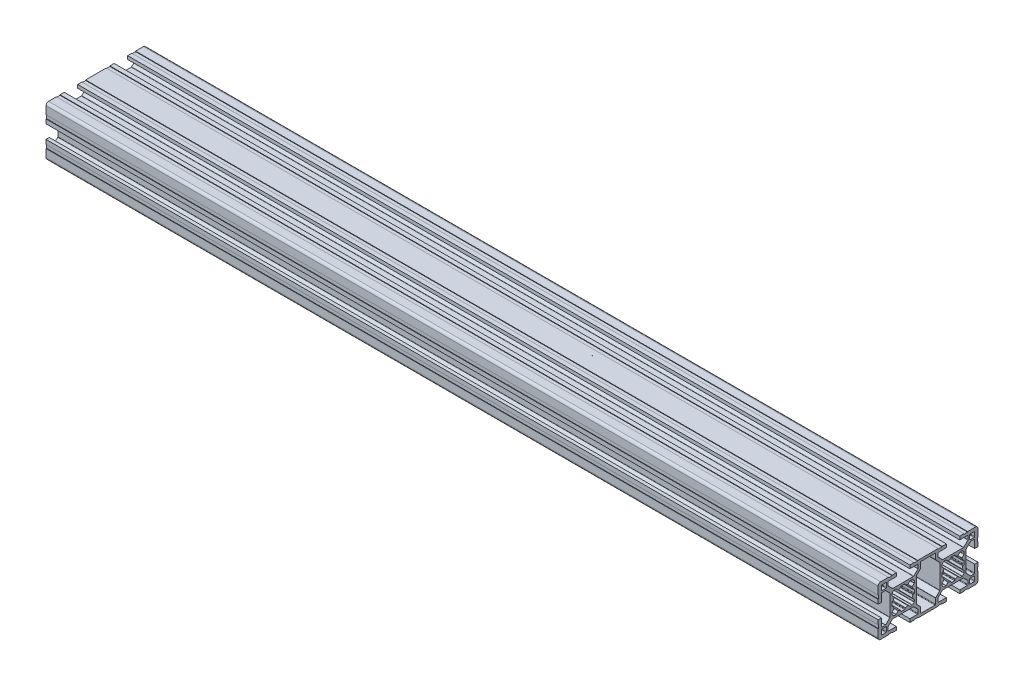
SolidWorks part; units mm, degrees
material "6063-T5 (Padrão)"
ref_plane "Plano frontal" through (0, 0, 0) normal (0, 0, 1) x (1, 0, 0)
ref_plane "Plano superior" through (0, 0, 0) normal (0, 1, 0) x (1, 0, 0)
ref_plane "Plano direito" through (0, 0, 0) normal (1, 0, 0) x (0, 0, -1)
sketch "Esboço1" plane through (0, 0, 0) normal (0, 0, 1) x (1, 0, 0)
  line L0 (-250, 0) -> (250, 0)
  point P4 (0, 0)
  dimension "D1" = 500
other "Retangular PF30-02 - PERFIL 3060 BÁSICO(1)"
ref_plane "Plano1" through (-250, 0, 0) normal (1, 0, 0) x (0, 1, 0)
sketch "Sketch11" plane through (-250, 0, 0) normal (1, 0, 0) x (0, 1, 0)
  line L0 (-9.8464, -4.5906) -> (-7.4222, -7.0149)
  line L1 (-7.21, -7.1028) -> (7.21, -7.1028)
  line L2 (7.4222, -7.0149) -> (9.8464, -4.5906)
  line L3 (10.0586, -4.5028) -> (13.2, -4.5028)
  line L4 (13.5, -4.2028) -> (13.5, 4.1972)
  line L5 (13.2, 4.4972) -> (10.0586, 4.4972)
  line L6 (9.8464, 4.5851) -> (7.4222, 7.0094)
  line L7 (7.21, 7.0972) -> (-7.21, 7.0972)
  line L8 (-7.4222, 7.0094) -> (-9.8464, 4.5851)
  line L9 (-10.0586, 4.4972) -> (-13.2, 4.4972)
  line L10 (-13.5, 4.1972) -> (-13.5, -4.2028)
  line L11 (-13.2, -4.5028) -> (-10.0586, -4.5028)
  line L12 (-6.7, 15.9528) -> (-6.7, 14.0528)
  line L13 (-6.1579, 16.2528) -> (-6.4, 16.2528)
  line L14 (-6.6121, 19.14) -> (-5.4871, 18.015)
  line L15 (-6.7, 20.4423) -> (-6.7, 19.3522)
  line L16 (-6.1319, 21.1347) -> (-6.6121, 20.6545)
  line L17 (-10.4678, 23.9149) -> (-7.9879, 21.435)
  line L18 (-12.7, 24.0028) -> (-10.6799, 24.0028)
  line L19 (-13, 19.0528) -> (-13, 23.7028)
  line L20 (-13, 19.0528) -> (-15, 19.0528)
  line L21 (6.7, 15.9528) -> (6.7, 14.0528)
  line L22 (7.9, 21.2229) -> (7.9, 8.7827)
  line L23 (15, 21.6028) -> (15, 19.0528)
  line L24 (-5.4396, 21.7028) -> (-4.3494, 21.7028)
  line L25 (-13, 25.3028) -> (-13, 27.7028)
  line L26 (-4.05, 28.0028) -> (-8.7, 28.0028)
  line L27 (-12.7, 28.0028) -> (-10.3, 28.0028)
  line L28 (-9, 27.7028) -> (-9, 25.6827)
  line L29 (-10, 27.7028) -> (-10, 25.3028)
  line L30 (-8.9121, 25.4705) -> (-6.4322, 22.9906)
  line L31 (15, 23.8028) -> (14.7, 23.8028)
  line L32 (14.7, 23.8028) -> (14.7, 21.6028)
  line L33 (15, 28.5028) -> (15, 23.8028)
  line L34 (8.8, 30.0028) -> (13.5, 30.0028)
  line L35 (8.8, 29.7028) -> (6.6, 29.7028)
  line L36 (4.05, 30.0028) -> (6.6, 30.0028)
  line L37 (4.05, 28.0028) -> (4.05, 30.0028)
  line L38 (10.3, 25.0028) -> (12.7, 25.0028)
  line L39 (15, 21.6028) -> (14.7, 21.6028)
  line L40 (6.6, 30.0028) -> (6.6, 29.7028)
  line L41 (-6.1319, 21.1347) -> (-5.6517, 21.6149)
  line L42 (-4.1373, 21.6149) -> (-3.0123, 20.4899)
  line L43 (-1.25, 21.1607) -> (-1.25, 21.4028)
  line L44 (8.8, 30.0028) -> (8.8, 29.7028)
  line L45 (1.25, 21.1607) -> (1.25, 21.4028)
  line L46 (4.1373, 21.6149) -> (3.0123, 20.4899)
  line L47 (6.1319, 21.1347) -> (5.6517, 21.6149)
  line L48 (8.9121, 25.4705) -> (6.4322, 22.9906)
  line L49 (10, 27.7028) -> (10, 25.3028)
  line L50 (9, 27.7028) -> (9, 25.6827)
  line L51 (12.7, 28.0028) -> (10.3, 28.0028)
  line L52 (4.05, 28.0028) -> (8.7, 28.0028)
  line L53 (13, 25.3028) -> (13, 27.7028)
  line L54 (5.4396, 21.7028) -> (4.3494, 21.7028)
  line L55 (13, 19.0528) -> (15, 19.0528)
  line L56 (13, 19.0528) -> (13, 23.7028)
  line L57 (12.7, 24.0028) -> (10.6799, 24.0028)
  line L58 (10.4678, 23.9149) -> (7.9879, 21.435)
  line L59 (6.1319, 21.1347) -> (6.6121, 20.6545)
  line L60 (6.7, 20.4423) -> (6.7, 19.3522)
  line L61 (6.6121, 19.14) -> (5.4871, 18.015)
  line L62 (6.1579, 16.2528) -> (6.4, 16.2528)
  line L63 (-7.9, 8.7827) -> (-7.9, 21.2229)
  line L64 (-0.95, 8.3028) -> (0.95, 8.3028)
  line L65 (-15, 8.4028) -> (-15, 10.9528)
  line L66 (-15, 6.2028) -> (-14.7, 6.2028)
  line L67 (-14.7, 6.2028) -> (-14.7, 8.4028)
  line L68 (-15, -14.9972) -> (15, -14.9972) construction
  line L69 (-6.1579, -13.7472) -> (-6.4, -13.7472)
  line L70 (-6.6121, -10.86) -> (-5.4871, -11.985)
  line L71 (-6.7, -9.5577) -> (-6.7, -10.6478)
  line L72 (-15, 8.4028) -> (-14.7, 8.4028)
  line L73 (-0.95, -21.6972) -> (0.95, -21.6972)
  line L74 (-6.1319, -8.8653) -> (-6.6121, -9.3455)
  line L75 (6.1579, 13.7528) -> (6.4, 13.7528)
  line L76 (6.6121, 10.8655) -> (5.4871, 11.9905)
  line L77 (6.7, 9.5632) -> (6.7, 10.6534)
  line L78 (6.1319, 8.8709) -> (6.6121, 9.3511)
  line L79 (10.4678, 6.0906) -> (7.9879, 8.5705)
  line L80 (12.7, 6.0028) -> (10.6799, 6.0028)
  line L81 (13, 10.9528) -> (13, 6.3028)
  line L82 (13, 10.9528) -> (15, 10.9528)
  line L83 (5.4396, 8.3028) -> (4.3494, 8.3028)
  line L84 (-10.4678, -6.0851) -> (-7.9879, -8.565)
  line L85 (-8.8, 30.0028) -> (-8.8, 29.7028)
  line L86 (-12.7, -5.9972) -> (-10.6799, -5.9972)
  line L87 (-13, -10.9472) -> (-13, -6.2972)
  line L88 (-13, -10.9472) -> (-15, -10.9472)
  line L89 (15, -8.3972) -> (15, -10.9472)
  line L90 (-5.4396, -8.2972) -> (-4.3494, -8.2972)
  line L91 (6.1319, 8.8709) -> (5.6517, 8.3906)
  line L92 (4.1373, 8.3906) -> (3.0123, 9.5156)
  line L93 (1.25, 8.8448) -> (1.25, 8.6028)
  line L94 (-15, -21.5972) -> (-15, -19.0472)
  line L95 (-6.6, 30.0028) -> (-6.6, 29.7028)
  line L96 (-1.25, 8.8448) -> (-1.25, 8.6028)
  line L97 (-4.1373, 8.3906) -> (-3.0123, 9.5156)
  line L98 (-6.1319, 8.8709) -> (-5.6517, 8.3906)
  line L99 (-15, -23.7972) -> (-14.7, -23.7972)
  line L100 (15, 8.4028) -> (14.7, 8.4028)
  line L101 (-14.7, -23.7972) -> (-14.7, -21.5972)
  line L102 (-15, -28.4972) -> (-15, -23.7972)
  line L103 (-8.8, -29.9972) -> (-13.5, -29.9972)
  line L104 (-8.8, -29.6972) -> (-6.6, -29.6972)
  line L105 (-4.05, -29.9972) -> (-6.6, -29.9972)
  line L106 (14.7, 6.2028) -> (14.7, 8.4028)
  line L107 (15, 6.2028) -> (14.7, 6.2028)
  line L108 (-4.05, -27.9972) -> (-4.05, -29.9972)
  line L109 (-10.3, -24.9972) -> (-12.7, -24.9972)
  line L110 (-6.2201, -22.8972) -> (6.2201, -22.8972)
  line L111 (-15, -21.5972) -> (-14.7, -21.5972)
  line L112 (15, -6.1972) -> (14.7, -6.1972)
  line L113 (-15, 21.6028) -> (-14.7, 21.6028)
  line L114 (-6.2201, 22.9028) -> (6.2201, 22.9028)
  line L115 (-10.3, 25.0028) -> (-12.7, 25.0028)
  line L116 (-4.05, 28.0028) -> (-4.05, 30.0028)
  line L117 (-4.05, 30.0028) -> (-6.6, 30.0028)
  line L118 (-8.8, 29.7028) -> (-6.6, 29.7028)
  line L119 (0, 29.9972) -> (0, -29.9972) construction
  line L120 (-15, 15.0028) -> (15, 15.0028) construction
  line L121 (-8.8, 30.0028) -> (-13.5, 30.0028)
  line L122 (-15, 28.5028) -> (-15, 23.8028)
  line L123 (-14.7, 23.8028) -> (-14.7, 21.6028)
  line L124 (-15, 23.8028) -> (-14.7, 23.8028)
  line L125 (-15, 21.6028) -> (-15, 19.0528)
  line L126 (14.7, -6.1972) -> (14.7, -8.3972)
  line L127 (-5.4396, 8.3028) -> (-4.3494, 8.3028)
  line L128 (15, 8.4028) -> (15, 10.9528)
  line L129 (15, 6.2028) -> (15, -6.1972)
  line L130 (-13, 10.9528) -> (-15, 10.9528)
  line L131 (-13, 10.9528) -> (-13, 6.3028)
  line L132 (-12.7, 6.0028) -> (-10.6799, 6.0028)
  line L133 (-10.4678, 6.0906) -> (-7.9879, 8.5705)
  line L134 (-6.1319, 8.8709) -> (-6.6121, 9.3511)
  line L135 (-0.95, 21.7028) -> (0.95, 21.7028)
  line L136 (-6.7, 9.5632) -> (-6.7, 10.6534)
  line L137 (-6.6121, 10.8655) -> (-5.4871, 11.9905)
  line L138 (-6.1579, 13.7528) -> (-6.4, 13.7528)
  line L139 (15, 0.0028) -> (-15, 0.0028) construction
  line L140 (15, -8.3972) -> (14.7, -8.3972)
  line L141 (-6.1319, -8.8653) -> (-5.6517, -8.3851)
  line L142 (-4.1373, -8.3851) -> (-3.0123, -9.5101)
  line L143 (-1.25, -8.8393) -> (-1.25, -8.5972)
  line L144 (-6.6, -29.9972) -> (-6.6, -29.6972)
  line L145 (1.25, -8.8393) -> (1.25, -8.5972)
  line L146 (4.1373, -8.3851) -> (3.0123, -9.5101)
  line L147 (6.1319, -8.8653) -> (5.6517, -8.3851)
  line L148 (-8.8, -29.9972) -> (-8.8, -29.6972)
  line L149 (5.4396, -8.2972) -> (4.3494, -8.2972)
  line L150 (13, -10.9472) -> (15, -10.9472)
  line L151 (13, -10.9472) -> (13, -6.2972)
  line L152 (12.7, -5.9972) -> (10.6799, -5.9972)
  line L153 (10.4678, -6.0851) -> (7.9879, -8.565)
  line L154 (6.1319, -8.8653) -> (6.6121, -9.3455)
  line L155 (6.7, -9.5577) -> (6.7, -10.6478)
  line L156 (6.6121, -10.86) -> (5.4871, -11.985)
  line L157 (6.1579, -13.7472) -> (6.4, -13.7472)
  line L158 (-15, -8.3972) -> (-14.7, -8.3972)
  line L159 (-15, 6.2028) -> (-15, -6.1972)
  line L160 (-14.7, -6.1972) -> (-14.7, -8.3972)
  line L161 (-15, -6.1972) -> (-14.7, -6.1972)
  line L162 (-15, -8.3972) -> (-15, -10.9472)
  line L163 (-0.95, -8.2972) -> (0.95, -8.2972)
  line L164 (-7.9, -8.7771) -> (-7.9, -21.2173)
  line L165 (6.1579, -16.2472) -> (6.4, -16.2472)
  line L166 (6.6121, -19.1345) -> (5.4871, -18.0095)
  line L167 (6.7, -20.4368) -> (6.7, -19.3466)
  line L168 (6.1319, -21.1291) -> (6.6121, -20.6489)
  line L169 (10.4678, -23.9094) -> (7.9879, -21.4295)
  line L170 (12.7, -23.9972) -> (10.6799, -23.9972)
  line L171 (13, -19.0472) -> (13, -23.6972)
  line L172 (13, -19.0472) -> (15, -19.0472)
  line L173 (5.4396, -21.6972) -> (4.3494, -21.6972)
  line L174 (13, -25.2972) -> (13, -27.6972)
  line L175 (4.05, -27.9972) -> (8.7, -27.9972)
  line L176 (12.7, -27.9972) -> (10.3, -27.9972)
  line L177 (9, -27.6972) -> (9, -25.6771)
  line L178 (10, -27.6972) -> (10, -25.2972)
  line L179 (8.9121, -25.465) -> (6.4322, -22.9851)
  line L180 (6.1319, -21.1291) -> (5.6517, -21.6093)
  line L181 (4.1373, -21.6093) -> (3.0123, -20.4844)
  line L182 (1.25, -21.1551) -> (1.25, -21.3972)
  line L183 (8.8, -29.9972) -> (8.8, -29.6972)
  line L184 (-1.25, -21.1551) -> (-1.25, -21.3972)
  line L185 (-4.1373, -21.6093) -> (-3.0123, -20.4844)
  line L186 (-6.1319, -21.1291) -> (-5.6517, -21.6093)
  line L187 (6.6, -29.9972) -> (6.6, -29.6972)
  line L188 (15, -21.5972) -> (14.7, -21.5972)
  line L189 (10.3, -24.9972) -> (12.7, -24.9972)
  line L190 (4.05, -27.9972) -> (4.05, -29.9972)
  line L191 (4.05, -29.9972) -> (6.6, -29.9972)
  line L192 (8.8, -29.6972) -> (6.6, -29.6972)
  line L193 (8.8, -29.9972) -> (13.5, -29.9972)
  line L194 (15, -28.4972) -> (15, -23.7972)
  line L195 (14.7, -23.7972) -> (14.7, -21.5972)
  line L196 (15, -23.7972) -> (14.7, -23.7972)
  line L197 (-8.9121, -25.465) -> (-6.4322, -22.9851)
  line L198 (-10, -27.6972) -> (-10, -25.2972)
  line L199 (-9, -27.6972) -> (-9, -25.6771)
  line L200 (-12.7, -27.9972) -> (-10.3, -27.9972)
  line L201 (-4.05, -27.9972) -> (-8.7, -27.9972)
  line L202 (-13, -25.2972) -> (-13, -27.6972)
  line L203 (-5.4396, -21.6972) -> (-4.3494, -21.6972)
  line L204 (15, -21.5972) -> (15, -19.0472)
  line L205 (7.9, -21.2173) -> (7.9, -8.7771)
  line L206 (6.7, -15.9472) -> (6.7, -14.0472)
  line L207 (-13, -19.0472) -> (-15, -19.0472)
  line L208 (-13, -19.0472) -> (-13, -23.6972)
  line L209 (-12.7, -23.9972) -> (-10.6799, -23.9972)
  line L210 (-10.4678, -23.9094) -> (-7.9879, -21.4295)
  line L211 (-6.1319, -21.1291) -> (-6.6121, -20.6489)
  line L212 (-6.7, -20.4368) -> (-6.7, -19.3466)
  line L213 (-6.6121, -19.1345) -> (-5.4871, -18.0095)
  line L214 (-6.1579, -16.2472) -> (-6.4, -16.2472)
  line L215 (-6.7, -15.9472) -> (-6.7, -14.0472)
  arc A0 (-9.8464, -4.5906) -> (-10.0586, -4.5028) centre (-10.0586, -4.8028) ccw
  arc A1 (-7.4222, -7.0149) -> (-7.21, -7.1028) centre (-7.21, -6.8028) ccw
  arc A2 (7.21, -7.1028) -> (7.4222, -7.0149) centre (7.21, -6.8028) ccw
  arc A3 (10.0586, -4.5028) -> (9.8464, -4.5906) centre (10.0586, -4.8028) ccw
  arc A4 (13.2, -4.5028) -> (13.5, -4.2028) centre (13.2, -4.2028) ccw
  arc A5 (13.5, 4.1972) -> (13.2, 4.4972) centre (13.2, 4.1972) ccw
  arc A6 (9.8464, 4.5851) -> (10.0586, 4.4972) centre (10.0586, 4.7972) ccw
  arc A7 (7.4222, 7.0094) -> (7.21, 7.0972) centre (7.21, 6.7972) ccw
  arc A8 (-7.21, 7.0972) -> (-7.4222, 7.0094) centre (-7.21, 6.7972) ccw
  arc A9 (-10.0586, 4.4972) -> (-9.8464, 4.5851) centre (-10.0586, 4.7972) ccw
  arc A10 (-13.2, 4.4972) -> (-13.5, 4.1972) centre (-13.2, 4.1972) ccw
  arc A11 (-13.5, -4.2028) -> (-13.2, -4.5028) centre (-13.2, -4.2028) ccw
  arc A12 (-6.4, 16.2528) -> (-6.7, 15.9528) centre (-6.4, 15.9528) ccw
  arc A13 (-5.867, 16.4795) -> (-6.1579, 16.2528) centre (-6.1579, 16.5528) cw
  arc A14 (-5.867, 16.4795) -> (-5.43, 17.6706) centre (0, 15.0028) cw
  arc A15 (-5.4871, 18.015) -> (-5.43, 17.6706) centre (-5.6993, 17.8029) cw
  arc A16 (-6.6121, 19.14) -> (-6.7, 19.3522) centre (-6.4, 19.3522) cw
  arc A17 (-6.6121, 20.6545) -> (-6.7, 20.4423) centre (-6.4, 20.4423) ccw
  arc A18 (-7.9879, 21.435) -> (-7.9, 21.2229) centre (-8.2, 21.2229) cw
  arc A19 (-10.6799, 24.0028) -> (-10.4678, 23.9149) centre (-10.6799, 23.7028) cw
  arc A20 (-13, 23.7028) -> (-12.7, 24.0028) centre (-12.7, 23.7028) cw
  arc A21 (13.5, 30.0028) -> (15, 28.5028) centre (13.5, 28.5028) cw
  arc A22 (1.25, 21.4028) -> (0.95, 21.7028) centre (0.95, 21.4028) ccw
  arc A23 (4.1373, 21.6149) -> (4.3494, 21.7028) centre (4.3494, 21.4028) cw
  arc A24 (1.4768, 20.8698) -> (1.25, 21.1607) centre (1.55, 21.1607) cw
  arc A25 (1.4768, 20.8698) -> (2.6678, 20.4328) centre (0, 15.0028) cw
  arc A26 (-10.3, 25.0028) -> (-10, 25.3028) centre (-10.3, 25.3028) ccw
  arc A27 (-6.4322, 22.9906) -> (-6.2201, 22.9028) centre (-6.2201, 23.2028) ccw
  arc A28 (-13, 25.3028) -> (-12.7, 25.0028) centre (-12.7, 25.3028) ccw
  arc A29 (-9, 25.6827) -> (-8.9121, 25.4705) centre (-8.7, 25.6827) ccw
  arc A30 (-10, 27.7028) -> (-10.3, 28.0028) centre (-10.3, 27.7028) ccw
  arc A31 (-8.7, 28.0028) -> (-9, 27.7028) centre (-8.7, 27.7028) ccw
  arc A32 (-12.7, 28.0028) -> (-13, 27.7028) centre (-12.7, 27.7028) ccw
  arc A33 (3.0123, 20.4899) -> (2.6678, 20.4328) centre (2.8001, 20.702) cw
  arc A34 (5.6517, 21.6149) -> (5.4396, 21.7028) centre (5.4396, 21.4028) ccw
  arc A35 (12.7, 28.0028) -> (13, 27.7028) centre (12.7, 27.7028) cw
  arc A36 (8.7, 28.0028) -> (9, 27.7028) centre (8.7, 27.7028) cw
  arc A37 (10, 27.7028) -> (10.3, 28.0028) centre (10.3, 27.7028) cw
  arc A38 (9, 25.6827) -> (8.9121, 25.4705) centre (8.7, 25.6827) cw
  arc A39 (13, 25.3028) -> (12.7, 25.0028) centre (12.7, 25.3028) cw
  arc A40 (6.4322, 22.9906) -> (6.2201, 22.9028) centre (6.2201, 23.2028) cw
  arc A41 (10.3, 25.0028) -> (10, 25.3028) centre (10.3, 25.3028) cw
  arc A42 (13, 23.7028) -> (12.7, 24.0028) centre (12.7, 23.7028) ccw
  arc A43 (10.6799, 24.0028) -> (10.4678, 23.9149) centre (10.6799, 23.7028) ccw
  arc A44 (7.9879, 21.435) -> (7.9, 21.2229) centre (8.2, 21.2229) ccw
  arc A45 (6.6121, 20.6545) -> (6.7, 20.4423) centre (6.4, 20.4423) cw
  arc A46 (6.6121, 19.14) -> (6.7, 19.3522) centre (6.4, 19.3522) ccw
  arc A47 (5.4871, 18.015) -> (5.43, 17.6706) centre (5.6993, 17.8029) ccw
  arc A48 (5.867, 16.4795) -> (5.43, 17.6706) centre (0, 15.0028) ccw
  arc A49 (5.867, 16.4795) -> (6.1579, 16.2528) centre (6.1579, 16.5528) ccw
  arc A50 (6.4, 16.2528) -> (6.7, 15.9528) centre (6.4, 15.9528) cw
  arc A51 (6.4, 13.7528) -> (6.7, 14.0528) centre (6.4, 14.0528) ccw
  arc A52 (-5.6517, 21.6149) -> (-5.4396, 21.7028) centre (-5.4396, 21.4028) cw
  arc A53 (-3.0123, 20.4899) -> (-2.6678, 20.4328) centre (-2.8001, 20.702) ccw
  arc A54 (-1.4768, 20.8698) -> (-2.6678, 20.4328) centre (0, 15.0028) ccw
  arc A55 (-1.4768, 20.8698) -> (-1.25, 21.1607) centre (-1.55, 21.1607) ccw
  arc A56 (-4.1373, 21.6149) -> (-4.3494, 21.7028) centre (-4.3494, 21.4028) ccw
  arc A57 (-6.4, 13.7528) -> (-6.7, 14.0528) centre (-6.4, 14.0528) cw
  arc A58 (-13.5, -29.9972) -> (-15, -28.4972) centre (-13.5, -28.4972) cw
  arc A59 (-1.25, 8.6028) -> (-0.95, 8.3028) centre (-0.95, 8.6028) ccw
  arc A60 (-4.1373, 8.3906) -> (-4.3494, 8.3028) centre (-4.3494, 8.6028) cw
  arc A61 (-1.4768, 9.1358) -> (-1.25, 8.8448) centre (-1.55, 8.8448) cw
  arc A62 (-1.4768, 9.1358) -> (-2.6678, 9.5728) centre (0, 15.0028) cw
  arc A63 (-3.0123, 9.5156) -> (-2.6678, 9.5728) centre (-2.8001, 9.3035) cw
  arc A64 (-5.6517, 8.3906) -> (-5.4396, 8.3028) centre (-5.4396, 8.6028) ccw
  arc A65 (5.867, 13.526) -> (6.1579, 13.7528) centre (6.1579, 13.4528) cw
  arc A66 (5.867, 13.526) -> (5.43, 12.3349) centre (0, 15.0028) cw
  arc A67 (5.4871, 11.9905) -> (5.43, 12.3349) centre (5.6993, 12.2026) cw
  arc A68 (6.6121, 10.8655) -> (6.7, 10.6534) centre (6.4, 10.6534) cw
  arc A69 (6.6121, 9.3511) -> (6.7, 9.5632) centre (6.4, 9.5632) ccw
  arc A70 (7.9879, 8.5705) -> (7.9, 8.7827) centre (8.2, 8.7827) cw
  arc A71 (10.6799, 6.0028) -> (10.4678, 6.0906) centre (10.6799, 6.3028) cw
  arc A72 (13, 6.3028) -> (12.7, 6.0028) centre (12.7, 6.3028) cw
  arc A73 (-5.867, -13.5205) -> (-6.1579, -13.7472) centre (-6.1579, -13.4472) cw
  arc A74 (-5.867, -13.5205) -> (-5.43, -12.3294) centre (0, -14.9972) cw
  arc A75 (-1.25, -21.3972) -> (-0.95, -21.6972) centre (-0.95, -21.3972) ccw
  arc A76 (-5.4871, -11.985) -> (-5.43, -12.3294) centre (-5.6993, -12.1971) cw
  arc A77 (-6.6121, -10.86) -> (-6.7, -10.6478) centre (-6.4, -10.6478) cw
  arc A78 (-6.6121, -9.3455) -> (-6.7, -9.5577) centre (-6.4, -9.5577) ccw
  arc A79 (-7.9879, -8.565) -> (-7.9, -8.7771) centre (-8.2, -8.7771) cw
  arc A80 (5.6517, 8.3906) -> (5.4396, 8.3028) centre (5.4396, 8.6028) cw
  arc A81 (3.0123, 9.5156) -> (2.6678, 9.5728) centre (2.8001, 9.3035) ccw
  arc A82 (-10.6799, -5.9972) -> (-10.4678, -6.0851) centre (-10.6799, -6.2972) cw
  arc A83 (-13, -6.2972) -> (-12.7, -5.9972) centre (-12.7, -6.2972) cw
  arc A84 (1.25, -8.5972) -> (0.95, -8.2972) centre (0.95, -8.5972) ccw
  arc A85 (4.1373, -8.3851) -> (4.3494, -8.2972) centre (4.3494, -8.5972) cw
  arc A86 (1.4768, -9.1302) -> (1.25, -8.8393) centre (1.55, -8.8393) cw
  arc A87 (1.4768, -9.1302) -> (2.6678, -9.5672) centre (0, -14.9972) cw
  arc A88 (3.0123, -9.5101) -> (2.6678, -9.5672) centre (2.8001, -9.2979) cw
  arc A89 (1.4768, 9.1358) -> (2.6678, 9.5728) centre (0, 15.0028) ccw
  arc A90 (1.4768, 9.1358) -> (1.25, 8.8448) centre (1.55, 8.8448) ccw
  arc A91 (4.1373, 8.3906) -> (4.3494, 8.3028) centre (4.3494, 8.6028) ccw
  arc A92 (1.25, 8.6028) -> (0.95, 8.3028) centre (0.95, 8.6028) cw
  arc A93 (5.6517, -8.3851) -> (5.4396, -8.2972) centre (5.4396, -8.5972) ccw
  arc A94 (-13, 6.3028) -> (-12.7, 6.0028) centre (-12.7, 6.3028) ccw
  arc A95 (-10.6799, 6.0028) -> (-10.4678, 6.0906) centre (-10.6799, 6.3028) ccw
  arc A96 (-7.9879, 8.5705) -> (-7.9, 8.7827) centre (-8.2, 8.7827) ccw
  arc A97 (-6.6121, 9.3511) -> (-6.7, 9.5632) centre (-6.4, 9.5632) cw
  arc A98 (-6.6121, 10.8655) -> (-6.7, 10.6534) centre (-6.4, 10.6534) ccw
  arc A99 (-5.4871, 11.9905) -> (-5.43, 12.3349) centre (-5.6993, 12.2026) ccw
  arc A100 (-1.25, 21.4028) -> (-0.95, 21.7028) centre (-0.95, 21.4028) cw
  arc A101 (-5.867, 13.526) -> (-5.43, 12.3349) centre (0, 15.0028) ccw
  arc A102 (-5.867, 13.526) -> (-6.1579, 13.7528) centre (-6.1579, 13.4528) ccw
  arc A103 (-13.5, 30.0028) -> (-15, 28.5028) centre (-13.5, 28.5028) ccw
  arc A104 (13, -6.2972) -> (12.7, -5.9972) centre (12.7, -6.2972) ccw
  arc A105 (10.6799, -5.9972) -> (10.4678, -6.0851) centre (10.6799, -6.2972) ccw
  arc A106 (7.9879, -8.565) -> (7.9, -8.7771) centre (8.2, -8.7771) ccw
  arc A107 (6.6121, -9.3455) -> (6.7, -9.5577) centre (6.4, -9.5577) cw
  arc A108 (6.6121, -10.86) -> (6.7, -10.6478) centre (6.4, -10.6478) ccw
  arc A109 (5.4871, -11.985) -> (5.43, -12.3294) centre (5.6993, -12.1971) ccw
  arc A110 (5.867, -13.5205) -> (5.43, -12.3294) centre (0, -14.9972) ccw
  arc A111 (5.867, -13.5205) -> (6.1579, -13.7472) centre (6.1579, -13.4472) ccw
  arc A112 (-5.6517, -8.3851) -> (-5.4396, -8.2972) centre (-5.4396, -8.5972) cw
  arc A113 (-3.0123, -9.5101) -> (-2.6678, -9.5672) centre (-2.8001, -9.2979) ccw
  arc A114 (-1.4768, -9.1302) -> (-2.6678, -9.5672) centre (0, -14.9972) ccw
  arc A115 (-1.4768, -9.1302) -> (-1.25, -8.8393) centre (-1.55, -8.8393) ccw
  arc A116 (-4.1373, -8.3851) -> (-4.3494, -8.2972) centre (-4.3494, -8.5972) ccw
  arc A117 (-1.25, -8.5972) -> (-0.95, -8.2972) centre (-0.95, -8.5972) cw
  arc A118 (-6.4, -13.7472) -> (-6.7, -14.0472) centre (-6.4, -14.0472) ccw
  arc A119 (-4.1373, -21.6093) -> (-4.3494, -21.6972) centre (-4.3494, -21.3972) cw
  arc A120 (-1.4768, -20.8642) -> (-1.25, -21.1551) centre (-1.55, -21.1551) cw
  arc A121 (-1.4768, -20.8642) -> (-2.6678, -20.4272) centre (0, -14.9972) cw
  arc A122 (-3.0123, -20.4844) -> (-2.6678, -20.4272) centre (-2.8001, -20.6965) cw
  arc A123 (-5.6517, -21.6093) -> (-5.4396, -21.6972) centre (-5.4396, -21.3972) ccw
  arc A124 (6.4, -13.7472) -> (6.7, -14.0472) centre (6.4, -14.0472) cw
  arc A125 (6.4, -16.2472) -> (6.7, -15.9472) centre (6.4, -15.9472) ccw
  arc A126 (5.867, -16.474) -> (6.1579, -16.2472) centre (6.1579, -16.5472) cw
  arc A127 (5.867, -16.474) -> (5.43, -17.6651) centre (0, -14.9972) cw
  arc A128 (5.4871, -18.0095) -> (5.43, -17.6651) centre (5.6993, -17.7974) cw
  arc A129 (6.6121, -19.1345) -> (6.7, -19.3466) centre (6.4, -19.3466) cw
  arc A130 (6.6121, -20.6489) -> (6.7, -20.4368) centre (6.4, -20.4368) ccw
  arc A131 (7.9879, -21.4295) -> (7.9, -21.2173) centre (8.2, -21.2173) cw
  arc A132 (10.6799, -23.9972) -> (10.4678, -23.9094) centre (10.6799, -23.6972) cw
  arc A133 (13, -23.6972) -> (12.7, -23.9972) centre (12.7, -23.6972) cw
  arc A134 (10.3, -24.9972) -> (10, -25.2972) centre (10.3, -25.2972) ccw
  arc A135 (6.4322, -22.9851) -> (6.2201, -22.8972) centre (6.2201, -23.1972) ccw
  arc A136 (13, -25.2972) -> (12.7, -24.9972) centre (12.7, -25.2972) ccw
  arc A137 (9, -25.6771) -> (8.9121, -25.465) centre (8.7, -25.6771) ccw
  arc A138 (10, -27.6972) -> (10.3, -27.9972) centre (10.3, -27.6972) ccw
  arc A139 (8.7, -27.9972) -> (9, -27.6972) centre (8.7, -27.6972) ccw
  arc A140 (12.7, -27.9972) -> (13, -27.6972) centre (12.7, -27.6972) ccw
  arc A141 (5.6517, -21.6093) -> (5.4396, -21.6972) centre (5.4396, -21.3972) cw
  arc A142 (3.0123, -20.4844) -> (2.6678, -20.4272) centre (2.8001, -20.6965) ccw
  arc A143 (-12.7, -27.9972) -> (-13, -27.6972) centre (-12.7, -27.6972) cw
  arc A144 (-8.7, -27.9972) -> (-9, -27.6972) centre (-8.7, -27.6972) cw
  arc A145 (-10, -27.6972) -> (-10.3, -27.9972) centre (-10.3, -27.6972) cw
  arc A146 (-9, -25.6771) -> (-8.9121, -25.465) centre (-8.7, -25.6771) cw
  arc A147 (-13, -25.2972) -> (-12.7, -24.9972) centre (-12.7, -25.2972) cw
  arc A148 (-6.4322, -22.9851) -> (-6.2201, -22.8972) centre (-6.2201, -23.1972) cw
  arc A149 (-10.3, -24.9972) -> (-10, -25.2972) centre (-10.3, -25.2972) cw
  arc A150 (1.4768, -20.8642) -> (2.6678, -20.4272) centre (0, -14.9972) ccw
  arc A151 (1.4768, -20.8642) -> (1.25, -21.1551) centre (1.55, -21.1551) ccw
  arc A152 (4.1373, -21.6093) -> (4.3494, -21.6972) centre (4.3494, -21.3972) ccw
  arc A153 (1.25, -21.3972) -> (0.95, -21.6972) centre (0.95, -21.3972) cw
  arc A154 (13.5, -29.9972) -> (15, -28.4972) centre (13.5, -28.4972) ccw
  arc A155 (-13, -23.6972) -> (-12.7, -23.9972) centre (-12.7, -23.6972) ccw
  arc A156 (-10.6799, -23.9972) -> (-10.4678, -23.9094) centre (-10.6799, -23.6972) ccw
  arc A157 (-7.9879, -21.4295) -> (-7.9, -21.2173) centre (-8.2, -21.2173) ccw
  arc A158 (-6.6121, -20.6489) -> (-6.7, -20.4368) centre (-6.4, -20.4368) cw
  arc A159 (-6.6121, -19.1345) -> (-6.7, -19.3466) centre (-6.4, -19.3466) ccw
  arc A160 (-5.4871, -18.0095) -> (-5.43, -17.6651) centre (-5.6993, -17.7974) ccw
  arc A161 (-5.867, -16.474) -> (-5.43, -17.6651) centre (0, -14.9972) ccw
  arc A162 (-5.867, -16.474) -> (-6.1579, -16.2472) centre (-6.1579, -16.5472) ccw
  arc A163 (-6.4, -16.2472) -> (-6.7, -15.9472) centre (-6.4, -15.9472) cw
  point P36 (-15, -14.9972)
  point P37 (0, 15.0028)
  point P66 (-11.6899, 24.0028)
  point P156 (0, 30.0028)
  point P176 (15, 30.0028)
  point P177 (11.6899, 24.0028)
  point P179 (-6.7, 15.0028)
  point P180 (6.7, 15.0028)
  point P187 (0, -0.0028)
  point P291 (15, -14.9972)
  point P315 (0, 29.9972)
  point P317 (15, 15.0028)
  point P321 (-15, 15.0028)
  point P322 (-15, 30.0028)
  point P324 (0, 15.0028)
  point P357 (-15, 0.0028)
  point P358 (0, 0.0083)
  point P359 (11.6899, 6.0028)
  point P360 (15, 0.0028)
  point P361 (0, 0.0028)
  point P362 (-11.6899, 6.0028)
  point P534 (0, -14.9972)
  point P539 (-15, -29.9972)
  point P557 (-11.6899, -5.9972)
  point P558 (11.6899, -5.9972)
  point P559 (0, -29.9917)
  point P560 (6.7, -14.9972)
  point P561 (-6.7, -14.9972)
  point P562 (11.6899, -23.9972)
  point P563 (15, -29.9972)
  point P564 (0, -29.9972)
  point P565 (-11.6899, -23.9972)
  point P566 (0, 0)
